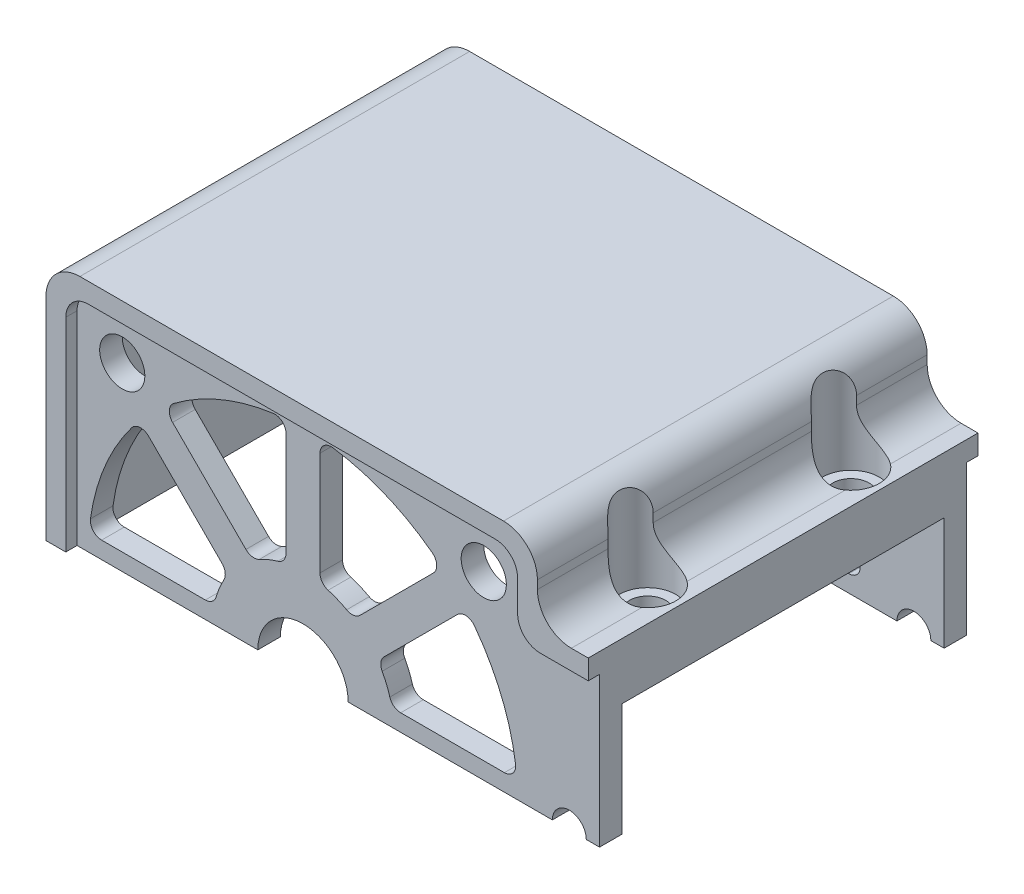
SolidWorks part; units mm, degrees
ref_plane "前视基准面" through (0, 0, 0) normal (0, 0, 1) x (1, 0, 0)
ref_plane "上视基准面" through (0, 0, 0) normal (0, 1, 0) x (1, 0, 0)
ref_plane "右视基准面" through (0, 0, 0) normal (1, 0, 0) x (0, 0, -1)
sketch "草图1" plane through (0, 0, 0) normal (0, 0, 1) x (1, 0, 0)
  line L5 (-20.25, 0) -> (-20.25, 17.25)
  line L6 (-17.25, 20.25) -> (17.25, 20.25)
  line L11 (23.25, 10) -> (26.25, 10)
  line L12 (20.25, 17.25) -> (20.25, 13)
  line L13 (-20.25, 0) -> (-21.75, 0)
  line L15 (0, 21.75) -> (-18.75, 21.75)
  line L16 (-21.75, 18.75) -> (-21.75, 0)
  line L17 (26.25, 10) -> (26.25, 15)
  line L21 (26.25, 15) -> (24.75, 15)
  line L22 (18.75, 21.75) -> (0, 21.75)
  line L23 (21.75, 18) -> (21.75, 18.75)
  arc A0 (24.75, 15) -> (21.75, 18) centre (24.75, 18) cw
  arc A1 (20.25, 13) -> (23.25, 10) centre (23.25, 13) ccw
  arc A2 (21.75, 18.75) -> (18.75, 21.75) centre (18.75, 18.75) ccw
  arc A3 (17.25, 20.25) -> (20.25, 17.25) centre (17.25, 17.25) cw
  arc A4 (-20.25, 17.25) -> (-17.25, 20.25) centre (-17.25, 17.25) cw
  arc A5 (-18.75, 21.75) -> (-21.75, 18.75) centre (-18.75, 18.75) ccw
  dimension "D1" = 3
extrude "凸台-拉伸1" add sketch "草图1" along normal blind 28.5
sketch "草图2" plane through (0, 0, 28.5) normal (0, 0, 1) x (1, 0, 0)
  line L0 (-21.75, 0) -> (26.25, 0)
  line L1 (26.25, 0) -> (26.25, 15)
  line L2 (26.25, 15) -> (24.75, 15)
  line L3 (21.75, 18) -> (21.75, 18.75)
  line L4 (18.75, 21.75) -> (-18.75, 21.75)
  line L5 (-21.75, 18.75) -> (-21.75, 0)
  arc A0 (24.75, 15) -> (21.75, 18) centre (24.75, 18) cw
  arc A1 (21.75, 18.75) -> (18.75, 21.75) centre (18.75, 18.75) ccw
  arc A2 (-18.75, 21.75) -> (-21.75, 18.75) centre (-18.75, 18.75) ccw
  dimension "D1" = 3
extrude "凸台-拉伸2" add sketch "草图2" along normal blind 3
sketch "草图3" plane through (0, 0, 0) normal (0, 0, -1) x (-1, 0, 0)
  line L0 (21.75, 0) -> (-26.25, 0)
  line L1 (-26.25, 0) -> (-26.25, 15)
  line L2 (-26.25, 15) -> (-24.75, 15)
  line L3 (-21.75, 18) -> (-21.75, 18.75)
  line L4 (-18.75, 21.75) -> (18.75, 21.75)
  line L5 (21.75, 18.75) -> (21.75, 0)
  arc A0 (-24.75, 15) -> (-21.75, 18) centre (-24.75, 18) ccw
  arc A1 (-21.75, 18.75) -> (-18.75, 21.75) centre (-18.75, 18.75) cw
  arc A2 (18.75, 21.75) -> (21.75, 18.75) centre (18.75, 18.75) cw
  dimension "D1" = 3
extrude "凸台-拉伸3" add sketch "草图3" along normal blind 3
sketch "草图4" plane through (0, 0, 31.5) normal (0, 0, 1) x (1, 0, 0)
  line L0 (26.25, 13.25) -> (26.25, 0)
  line L1 (-21.75, 0) -> (26.25, 0) construction
  line L2 (-20, 0) -> (-20, 18)
  line L3 (-18, 20) -> (18, 20)
  line L4 (26.25, 0) -> (-20, 0)
  line L5 (26.25, 0) -> (26.25, 15) construction
  line L6 (26.25, 13.25) -> (22, 13.25)
  line L7 (20, 15.25) -> (20, 18)
  arc A0 (18, 20) -> (20, 18) centre (18, 18) cw
  arc A1 (22, 13.25) -> (20, 15.25) centre (22, 15.25) cw
  arc A2 (-20, 18) -> (-18, 20) centre (-18, 18) cw
  dimension "D1" = 2
extrude "切除-拉伸1" cut sketch "草图4" against normal blind 1
sketch "草图5" plane through (0, 0, -3) normal (0, 0, -1) x (-1, 0, 0)
  line L0 (0, 0) -> (20, 0)
  line L1 (-26.25, 0) -> (21.75, 0) construction
  line L2 (20, 0) -> (20, 18)
  line L3 (18, 20) -> (-18, 20)
  line L4 (0, 0) -> (-26.25, 0)
  line L5 (-26.25, 15) -> (-26.25, 0) construction
  line L6 (-26.25, 13.25) -> (-22, 13.25)
  line L7 (-20, 15.25) -> (-20, 18)
  line L8 (-26.25, 0) -> (-26.25, 13.25)
  arc A0 (-22, 13.25) -> (-20, 15.25) centre (-22, 15.25) ccw
  arc A1 (-18, 20) -> (-20, 18) centre (-18, 18) ccw
  arc A2 (20, 18) -> (18, 20) centre (18, 18) ccw
  dimension "D1" = 2
extrude "切除-拉伸2" cut sketch "草图5" against normal blind 1
sketch "草图6" plane through (0, 0, 30.5) normal (0, 0, 1) x (1, 0, 0)
  line L0 (22.074, 0) -> (25.074, 0)
  line L36 (-11.5439, 13.6652) -> (-5.0528, 7.1742)
  line L39 (-1.5, 17.8255) -> (-1.5, 8.6458)
  line L40 (1.5, 17.8255) -> (1.5, 8.6458)
  line L43 (11.5439, 13.6652) -> (5.0528, 7.1742)
  line L44 (13.6652, 11.5439) -> (7.1742, 5.0528)
  line L47 (17.8255, 1.5) -> (8.6458, 1.5)
  line L52 (-4, 0) -> (4, 0)
  line L53 (-17.8255, 1.5) -> (-8.6458, 1.5)
  line L58 (-13.6652, 11.5439) -> (-7.1742, 5.0528)
  circle A0 centre (-16, 16) radius 2
  circle A1 centre (16, 16) radius 2
  arc A3 (22.074, 0) -> (25.074, 0) centre (23.574, 0) cw
  arc A7 (-4, 0) -> (4, 0) centre (0, 0) cw
  arc A9 (18.8159, 2.6389) -> (17.8255, 1.5) centre (17.8255, 2.5) cw
  arc A35 (-18.8159, 2.6389) -> (-15.1708, 11.4388) centre (0, 0) cw
  arc A36 (-7.6852, 2.2222) -> (-7.0056, 3.8629) centre (0, 0) cw
  arc A37 (-3.8629, 7.0056) -> (-2.2222, 7.6852) centre (0, 0) cw
  arc A38 (2.2222, 7.6852) -> (3.8629, 7.0056) centre (0, 0) cw
  arc A39 (7.0056, 3.8629) -> (7.6852, 2.2222) centre (0, 0) cw
  arc A40 (-11.4388, 15.1708) -> (-2.6389, 18.8159) centre (0, 0) cw
  arc A41 (2.6389, 18.8159) -> (11.4388, 15.1708) centre (0, 0) cw
  arc A42 (15.1708, 11.4388) -> (18.8159, 2.6389) centre (0, 0) cw
  arc A45 (13.6652, 11.5439) -> (15.1708, 11.4388) centre (14.3723, 10.8368) cw
  arc A46 (11.4388, 15.1708) -> (11.5439, 13.6652) centre (10.8368, 14.3723) cw
  arc A47 (1.5, 17.8255) -> (2.6389, 18.8159) centre (2.5, 17.8255) cw
  arc A48 (-1.5, 17.8255) -> (-2.6389, 18.8159) centre (-2.5, 17.8255) ccw
  arc A49 (-11.5439, 13.6652) -> (-11.4388, 15.1708) centre (-10.8368, 14.3723) cw
  arc A50 (7.6852, 2.2222) -> (8.6458, 1.5) centre (8.6458, 2.5) ccw
  arc A51 (7.0056, 3.8629) -> (7.1742, 5.0528) centre (7.8813, 4.3457) cw
  arc A52 (3.8629, 7.0056) -> (5.0528, 7.1742) centre (4.3457, 7.8813) ccw
  arc A53 (1.5, 8.6458) -> (2.2222, 7.6852) centre (2.5, 8.6458) ccw
  arc A54 (-1.5, 8.6458) -> (-2.2222, 7.6852) centre (-2.5, 8.6458) cw
  arc A55 (-3.8629, 7.0056) -> (-5.0528, 7.1742) centre (-4.3457, 7.8813) cw
  arc A56 (-7.0056, 3.8629) -> (-7.1742, 5.0528) centre (-7.8813, 4.3457) ccw
  arc A57 (-7.6852, 2.2222) -> (-8.6458, 1.5) centre (-8.6458, 2.5) cw
  arc A58 (-17.8255, 1.5) -> (-18.8159, 2.6389) centre (-17.8255, 2.5) cw
  arc A59 (-15.1708, 11.4388) -> (-13.6652, 11.5439) centre (-14.3723, 10.8368) cw
  point P72 (0, 0)
  dimension "D1" = 1
extrude "切除-拉伸3" cut sketch "草图6" against normal blind 33
sketch "草图7" plane through (0, 15, 0) normal (0, 1, 0) x (1, 0, 0)
  circle A0 centre (23.25, -5.25) radius 1.6
  circle A1 centre (23.25, -23.25) radius 1.6
extrude "切除-拉伸5" cut sketch "草图7" along normal blind 6 and the other way blind 6
sketch "草图8" plane through (0, 15, 0) normal (0, 1, 0) x (1, 0, 0)
  circle A0 centre (23.25, -5.25) radius 2.5
  circle A1 centre (23.25, -23.25) radius 2.5
extrude "切除-拉伸6" cut sketch "草图8" along normal blind 6 and the other way blind 2
